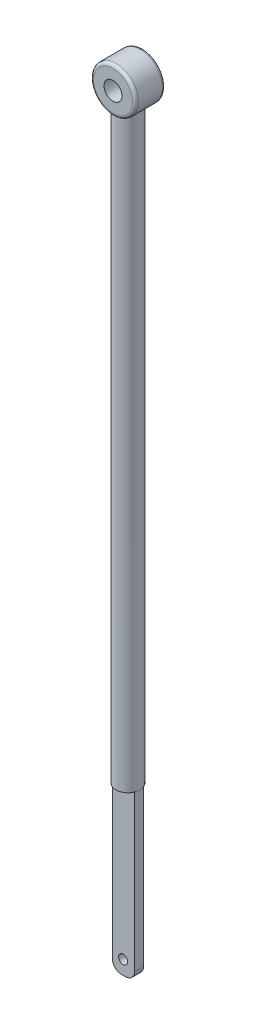
SolidWorks part; units mm, degrees
ref_plane "前视基准面" through (0, 0, 0) normal (0, 0, 1) x (1, 0, 0)
ref_plane "上视基准面" through (0, 0, 0) normal (0, 1, 0) x (1, 0, 0)
ref_plane "右视基准面" through (0, 0, 0) normal (1, 0, 0) x (0, 0, -1)
sketch "草图1" plane through (0, 0, 0) normal (0, 0, 1) x (1, 0, 0)
  line L0 (0.9823, 0.1898) -> (0.75, 0)
  circle A1 centre (0.75, 0) radius 0.3
  circle A2 centre (0.75, 0) radius 0.75
extrude "凸台-拉伸1" add sketch "草图1" along normal blind 1 contours A2 A1
fillet "圆角1" radius 0.1 2 edges at (1.5, 0, 0) (1.5, 0, 1)
ref_plane "基准面1" through (0, -0.3, 0) normal (0, 1, 0) x (-1, 0, 0)
sketch "草图2" plane through (0, -0.3, 0) normal (0, 1, 0) x (-1, 0, 0)
  line L0 (-1.5, 0.9) -> (0, 0.1)
  circle A0 centre (-0.75, 0.5) radius 0.4
extrude "凸台-拉伸2" add sketch "草图2" against normal blind 40 contours L0 A0 | L0 A0
sketch "草图3" plane through (0, -40.3, 0) normal (0, -1, 0) x (1, 0, 0)
  circle A0 centre (0.75, 0.5) radius 2.9535
extrude "切除-拉伸1" cut sketch "草图3" against normal blind 20
sketch "草图4" plane through (0, -20.3, 0) normal (0, -1, 0) x (1, 0, 0)
  line L1 (0.3792, 0.65) -> (1.1208, 0.65)
  line L2 (0.3792, 0.65) -> (0.3792, 0.35)
  line L3 (0.3792, 0.35) -> (1.1208, 0.35)
  line L4 (1.1208, 0.65) -> (1.1208, 0.35)
  line L5 (0.3792, 0.65) -> (1.1208, 0.35) construction
  line L6 (0.3792, 0.35) -> (1.1208, 0.65) construction
  circle A1 centre (0.75, 0.5) radius 0.4 construction
  point P0 (0.75, 0.5)
  point P1 (0.75, 0.5)
  dimension "D1" = 0.3
extrude "凸台-拉伸3" add sketch "草图4" along normal blind 5.5
sketch "草图6" plane through (0, 0, 0.35) normal (0, 0, -1) x (-1, 0, 0)
  circle A0 centre (-0.7376, -25.3363) radius 0.15
  dimension "D1" = 0.3
extrude "切除-拉伸2" cut sketch "草图6" against normal blind 5.5
fillet "圆角2" radius 0.3 2 edges at (1.1208, -25.8, 0.5) (0.3792, -25.8, 0.5)
